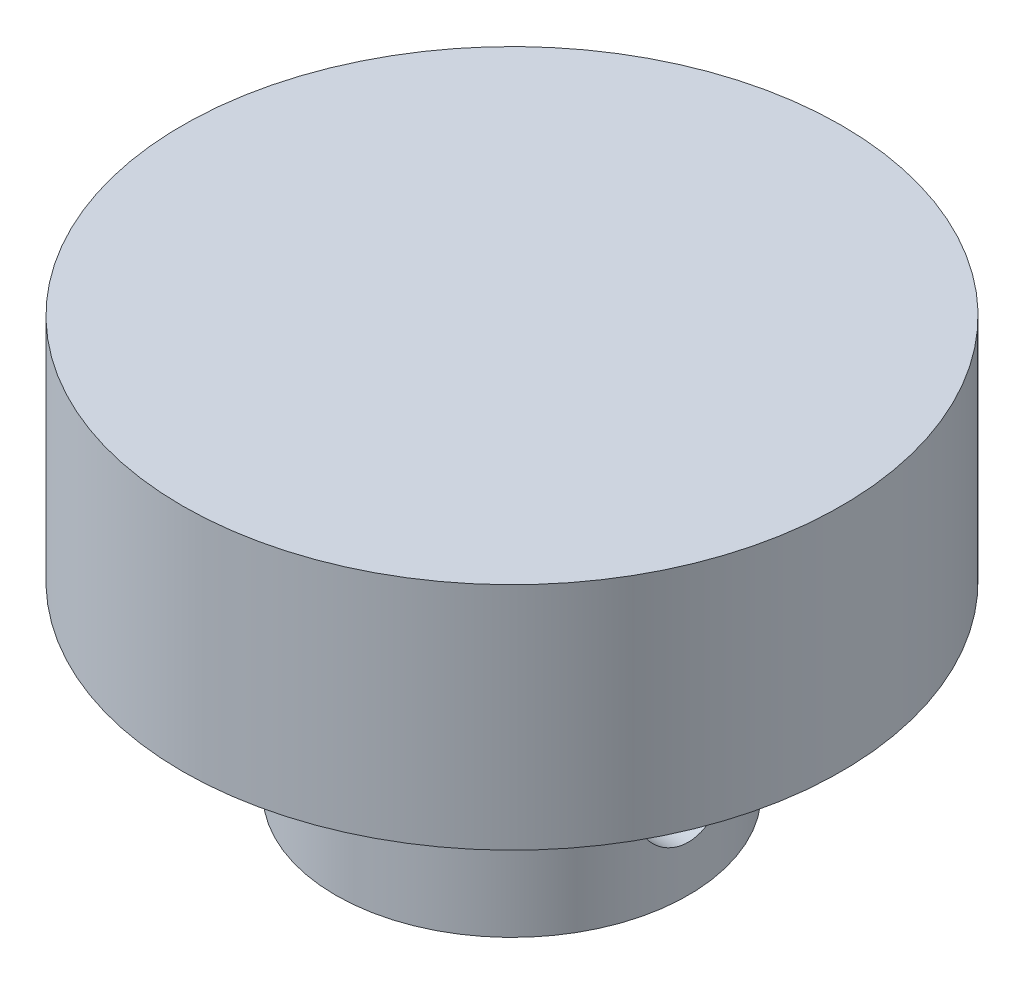
SolidWorks part; units mm, degrees
ref_plane "Front Plane" through (0, 0, 0) normal (0, 0, 1) x (1, 0, 0)
ref_plane "Top Plane" through (0, 0, 0) normal (0, 1, 0) x (1, 0, 0)
ref_plane "Right Plane" through (0, 0, 0) normal (1, 0, 0) x (0, 0, -1)
sketch "Sketch1" plane through (0, 0, 0) normal (1, 0, 0) x (0, 0, -1)
  line L0 (0, 0) -> (0, 11089.3826) construction
  line L1 (2, 0) -> (21.5, 0)
  line L2 (21.5, 0) -> (21.5, -15)
  line L3 (21.5, -15) -> (11.5, -15)
  line L4 (11.5, -15) -> (11.5, -27)
  line L5 (11.5, -27) -> (2, -27)
  line L6 (2, -27) -> (2, -15)
  line L7 (2, 0) -> (0, 0)
  line L8 (0, 0) -> (0, -15)
  line L9 (0, -15) -> (2, -15)
  point P7 (2, -21)
  dimension "D1" = 19.5
  dimension "D2" = 2
  dimension "D3" = 15
  dimension "D4" = 12
  dimension "D5" = 9.5
  dimension "D6" = 6
revolve "Revolve1" add sketch "Sketch1" angle 360 about L0
sketch "Sketch4" plane through (0, 0, 0) normal (1, 0, 0) x (0, 0, -1)
  line L0 (0, -27) -> (0, -15) construction
  line L1 (-11.5, -27) -> (11.5, -27) construction
  line L2 (-11.5, -15) -> (11.5, -15) construction
  line L3 (0, -21) -> (-17.6083, -21) construction
  circle A0 centre (0, -21) radius 3
extrude "Cut-Extrude2" cut sketch "Sketch4" against normal blind 13 and the other way blind 15 contours A0
